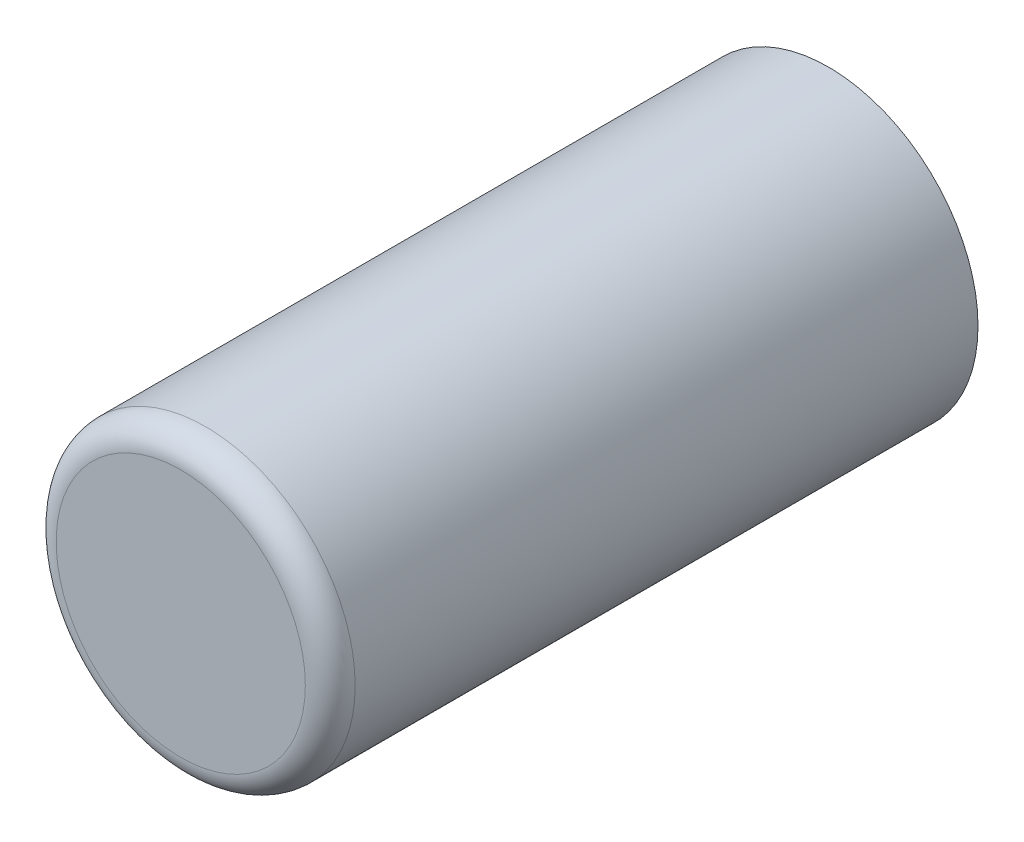
SolidWorks part; units mm, degrees
ref_plane "Front Plane" through (0, 0, 0) normal (0, 0, 1) x (1, 0, 0)
ref_plane "Top Plane" through (0, 0, 0) normal (0, 1, 0) x (1, 0, 0)
ref_plane "Right Plane" through (0, 0, 0) normal (1, 0, 0) x (0, 0, -1)
sketch "Sketch1" plane through (0, 0, 0) normal (0, 0, 1) x (1, 0, 0)
  circle A0 centre (0, 0) radius 4.8
  dimension "D1" = 9.6
extrude "Boss-Extrude1" add sketch "Sketch1" along normal mid plane 20.8
fillet "Fillet1" radius 0.8 1 edges at (4.8, 0, 10.4)
